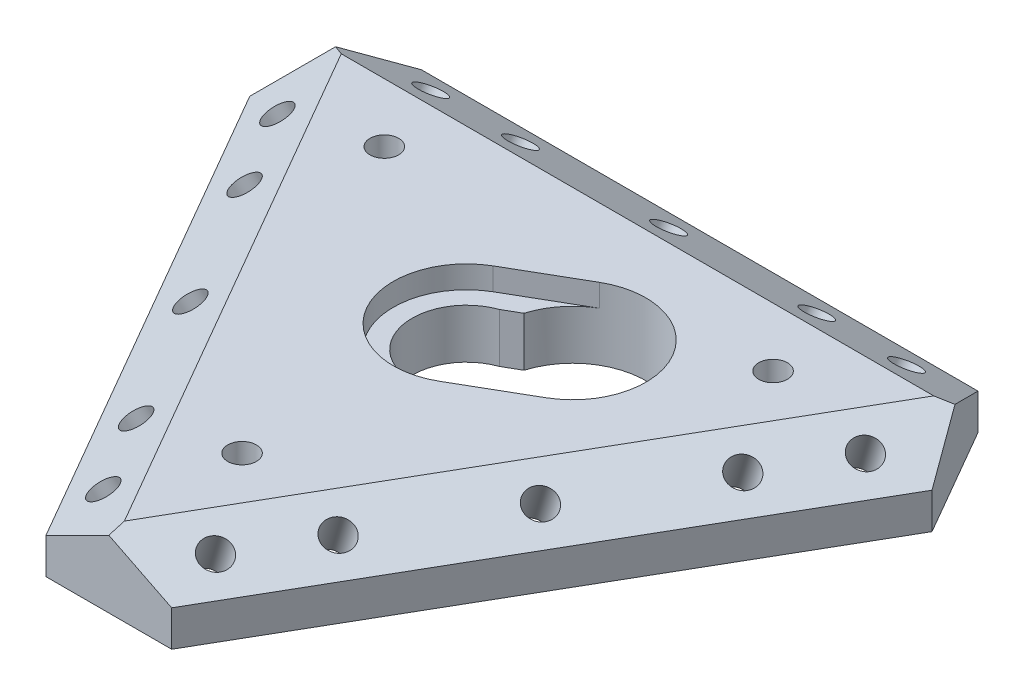
SolidWorks part; units mm, degrees
ref_plane "Front Plane" through (0, 0, 0) normal (0, 0, 1) x (1, 0, 0)
ref_plane "Top Plane" through (0, 0, 0) normal (0, 1, 0) x (1, 0, 0)
ref_plane "Right Plane" through (0, 0, 0) normal (1, 0, 0) x (0, 0, -1)
sketch "Sketch1" plane through (0, 0, 0) normal (0, 1, 0) x (1, 0, 0)
  line L0 (-31, 25.9808) -> (31, 25.9808)
  line L1 (31, 25.9808) -> (38, 13.8564)
  line L2 (38, 13.8564) -> (7, -39.8372)
  line L3 (7, -39.8372) -> (-7, -39.8372)
  line L4 (-7, -39.8372) -> (-38, 13.8564)
  line L5 (-38, 13.8564) -> (-31, 25.9808)
  line L6 (0, 0) -> (34.5, 19.9186) construction
  line L7 (0, 0) -> (0, -25.5) construction
  line L8 (3.9237, -4.6051) -> (5.6557, -3.6051)
  line L9 (-2.0263, 5.7006) -> (-0.2943, 6.7006)
  circle A0 centre (0, 0) radius 25.9808 construction
  arc A1 (-2.0263, 5.7006) -> (3.9237, -4.6051) centre (0, 0) ccw
  arc A2 (5.6557, -3.6051) -> (-0.2943, 6.7006) centre (7.5041, 4.3325) ccw
  point P14 (0, 0)
  point P28 (0, 0)
  dimension "D4" = 16.3
  dimension "D6" = 11.9
  dimension "D8" = 2
  dimension "D2" = 12.1
  dimension "D1" = 120
  dimension "D3" = 14
  dimension "D5" = 25.5
  dimension "D7" = 62
extrude "Boss-Extrude1" add sketch "Sketch1" along normal blind 8
chamfer "Chamfer1" distance 4 angle 60 3 edges at (22.5, 8, 12.9904) (-22.5, 8, 12.9904) (0, 8, -25.9808)
sketch "Sketch2" plane through (7.125, 14.25, 4.1136) normal (0.433, 0.866, 0.25) x (0.9014, -0.416, -0.1201)
  line L0 (28.4284, 12.8968) -> (-0.9707, -31.2019) construction
  line L1 (34.2527, 14.4222) -> (-0.1387, -37.1649) construction
  line L2 (28.4284, 12.8968) -> (34.2527, 14.4222) construction
  line L3 (-0.9707, -31.2019) -> (-0.1387, -37.1649) construction
  line L4 (28.4284, 12.8968) -> (31.7566, 10.678) construction
  line L5 (28.4284, 12.8968) -> (25.1002, 15.1156) construction
  line L6 (-7.9045, -34.3914) -> (28.7057, 20.5239) construction
  circle A0 centre (28.4284, 12.8968) radius 1.6
  circle A1 centre (-0.9707, -31.2019) radius 1.6
  circle A2 centre (13.7288, -9.1526) radius 1.6
  circle A3 centre (22.8814, 4.5763) radius 1.6
  circle A4 centre (28.4284, 12.8968) radius 5 construction
  circle A5 centre (4.5763, -22.8814) radius 1.6
  dimension "D1" = 3.2
  dimension "D6" = 10
  dimension "D2" = 53
  dimension "D3" = 10
  dimension "D4" = 10
extrude "Cut-Extrude1" cut sketch "Sketch2" against normal up to next
sketch "Sketch3" plane through (7.125, 14.25, 4.1136) normal (0.433, 0.866, 0.25) x (0.9014, -0.416, -0.1201)
  circle A0 centre (28.4284, 12.8968) radius 3
  circle A1 centre (-0.9707, -31.2019) radius 3
  circle A2 centre (13.7288, -9.1526) radius 3
  circle A3 centre (22.8814, 4.5763) radius 3
  circle A4 centre (4.5763, -22.8814) radius 3
  dimension "D1" = 6
extrude "Cut-Extrude2" cut sketch "Sketch3" against normal up to next from offset 6 offset against normal yes
pattern_circular "CirPattern1" count 3 every 120 about axis through (0, 0, 0) along (0, 1, 0) of "Cut-Extrude1", "Cut-Extrude2"
sketch "Sketch8" plane through (0, 8, 0) normal (0, 1, 0) x (1, 0, 0)
  line L0 (-4.075, 7.0581) -> (3.4291, 11.3906)
  line L1 (4.075, -7.0581) -> (11.5791, -2.7256)
  arc A0 (-4.075, 7.0581) -> (4.075, -7.0581) centre (0, 0) ccw
  arc A1 (11.5791, -2.7256) -> (3.4291, 11.3906) centre (7.5041, 4.3325) ccw
  arc A2 (5.6557, -3.6051) -> (-0.2943, 6.7006) centre (7.5041, 4.3325) ccw construction
extrude "Cut-Extrude4" cut sketch "Sketch8" against normal offset from surface (2.5 mm away) 5.5 up to face at (-24.0538, 0, -5.1651)
sketch "Sketch10" plane through (0, 8, 0) normal (0, 1, 0) x (1, 0, 0)
  line L0 (0, 0) -> (3.0258, 1.7469) construction
  line L1 (0, 0) -> (-2.9895, 1.726) construction
  line L2 (0, 0) -> (0, -4.6015) construction
  line L3 (33, 19.0526) -> (34.5, 19.9186) construction
  line L4 (-34.5, 19.9186) -> (-33, 19.0526) construction
  line L5 (0, -39.8372) -> (0, -38.1051) construction
  circle A0 centre (21.6506, 12.5) radius 1.6
  circle A1 centre (0, -25) radius 1.6
  circle A2 centre (-21.6506, 12.5) radius 1.6
  point P19 (0, 0)
  dimension "D1" = 3.2
  dimension "D2" = 25
  dimension "D3" = 3
extrude "Cut-Extrude5" cut sketch "Sketch10" against normal up to next
equation "\"D4@Sketch2\"=\"D3@Sketch2\""
